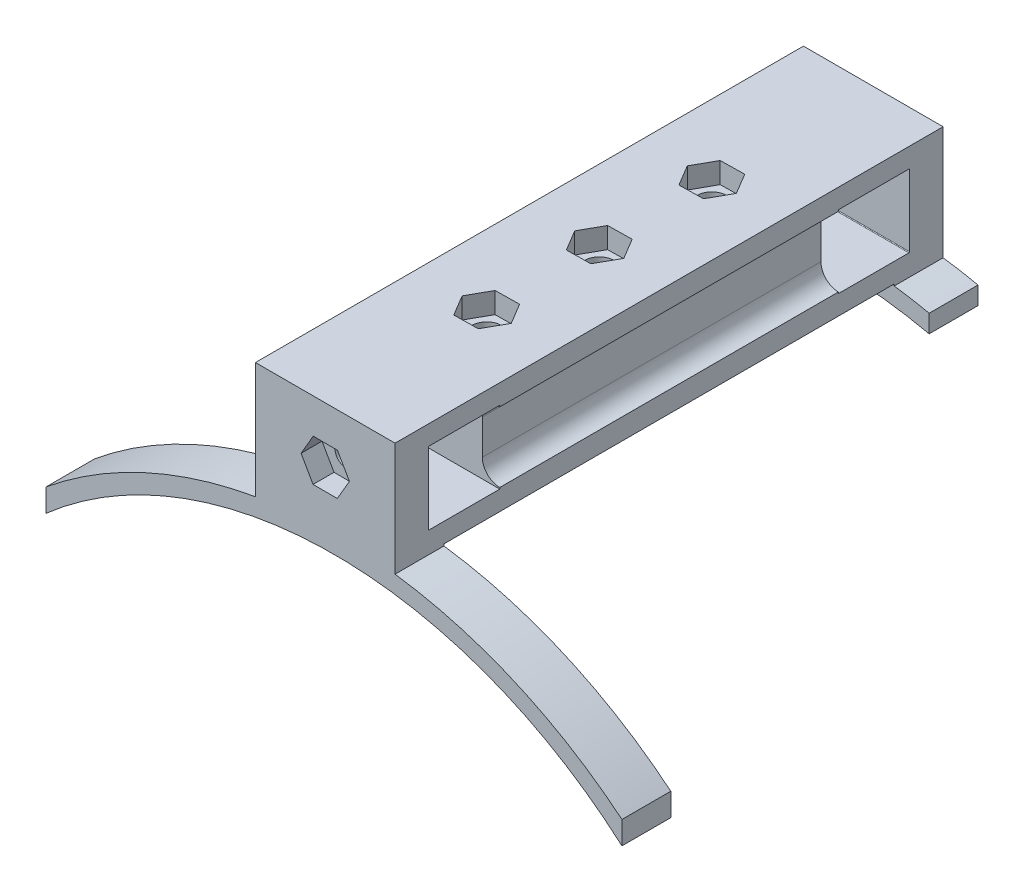
SolidWorks part; units mm, degrees
ref_plane "Front Plane" through (0, 0, 0) normal (0, 0, 1) x (1, 0, 0)
ref_plane "Top Plane" through (0, 0, 0) normal (0, 1, 0) x (1, 0, 0)
ref_plane "Right Plane" through (0, 0, 0) normal (1, 0, 0) x (0, 0, -1)
sketch "Sketch1" plane through (0, 0, 0) normal (0, 0, 1) x (1, 0, 0)
  line L0 (-2.0278, -2.1111) -> (-2.0278, 2.8889)
  line L2 (0.4722, 8.3889) -> (0.4722, 5.3889)
  line L3 (0.4722, -7.6111) -> (0.4722, -4.6111)
  line L9 (0.4722, 8.3889) -> (-17.5278, 8.3889)
  line L10 (0.4722, 8.3889) -> (0.4722, 5.3889)
  line L12 (0.4722, -7.6111) -> (-17.5278, -7.6111)
  line L13 (-17.5278, 8.3889) -> (-17.5278, -7.6111)
  line L14 (0.4722, 8.3889) -> (-17.5278, -7.6111) construction
  line L15 (0.4722, -7.6111) -> (-17.5278, 8.3889) construction
  line L17 (0.4722, -4.6111) -> (0.4722, -7.6111)
  arc A0 (0.4722, 5.3889) -> (-2.0278, 2.8889) centre (0.4722, 2.8889) ccw
  arc A1 (-2.0278, -2.1111) -> (0.4722, -4.6111) centre (0.4722, -2.1111) ccw
  point P14 (-8.5278, 0.3889)
  dimension "D2" = 18
extrude "Boss-Extrude2" add sketch "Sketch1" along normal blind 48.5 contours A1 L0 A0 L2 L9 L13 L12 L3
sketch "Sketch2" plane through (-17.5278, 0, 0) normal (-1, 0, 0) x (0, 0, 1)
  line L0 (48.5, 8.3889) -> (62.5, 8.3889)
  line L1 (63.5, 7.3889) -> (63.5, -6.6111)
  line L2 (62.5, -7.6111) -> (48.5, -7.6111)
  line L3 (58.5, -4.6111) -> (58.5, 5.3889) construction
  line L4 (62.5, 8.3889) -> (63.5, 8.3889)
  line L5 (63.5, 8.3889) -> (63.5, 7.3889)
  line L6 (48.5, 5.3889) -> (58.5, 5.3889) construction
  line L7 (58.5, -4.6111) -> (48.5, -4.6111) construction
  line L8 (48.5, 8.3889) -> (48.5, -7.6111) construction
  line L9 (48.5, 5.5889) -> (58.6, 5.5889)
  line L10 (58.7, -4.7111) -> (58.7, 5.4889)
  line L11 (58.6, -4.8111) -> (48.5, -4.8111)
  line L12 (48.5, 8.3889) -> (48.5, 5.5889)
  line L13 (48.5, -4.8111) -> (48.5, -7.6111)
  line L14 (24.25, 8.3889) -> (24.25, 19.6589) construction
  line L15 (48.5, 8.3889) -> (0, 8.3889) construction
  line L16 (0, -4.8111) -> (0, -7.6111)
  line L17 (0, 8.3889) -> (0, 5.5889)
  line L18 (-10.1, -4.8111) -> (0, -4.8111)
  line L19 (-10.2, -4.7111) -> (-10.2, 5.4889)
  line L20 (0, 5.5889) -> (-10.1, 5.5889)
  line L21 (-14, -7.6111) -> (0, -7.6111)
  line L22 (-15, 7.3889) -> (-15, -6.6111)
  line L23 (0, 8.3889) -> (-14, 8.3889)
  line L24 (63.5, -6.6111) -> (63.5, -7.6111)
  line L25 (63.5, -7.6111) -> (62.5, -7.6111)
  line L26 (-15, 7.3889) -> (-15, 8.3889)
  line L27 (-15, 8.3889) -> (-14, 8.3889)
  line L28 (-15, -6.6111) -> (-15, -7.6111)
  line L29 (-15, -7.6111) -> (-14, -7.6111)
  arc A0 (58.7, -4.7111) -> (58.6, -4.8111) centre (58.6, -4.7111) cw
  arc A1 (58.6, 5.5889) -> (58.7, 5.4889) centre (58.6, 5.4889) cw
  arc A6 (-10.1, 5.5889) -> (-10.2, 5.4889) centre (-10.1, 5.4889) ccw
  arc A7 (-10.2, -4.7111) -> (-10.1, -4.8111) centre (-10.1, -4.7111) ccw
  dimension "D5" = 0.1
  dimension "D1" = 5
  dimension "D2" = 0.2
  dimension "D3" = 0.2
  dimension "D4" = 0.2
extrude "Boss-Extrude3" add sketch "Sketch2" against normal blind 18
sketch "Sketch3" plane through (0, 0, 63.5) normal (0, 0, 1) x (1, 0, 0)
  circle A0 centre (-9.5278, 0.3889) radius 1.6
  dimension "D1" = 3.2
extrude "Cut-Extrude1" cut sketch "Sketch3" against normal blind 8
ref_plane "Plane1" through (0, 0, 24.25) normal (0, 0, 1) x (1, 0, 0)
mirror "Mirror1" about plane through (0, 0, 24.25) normal (0, 0, 1) of "Cut-Extrude1"
sketch "Sketch4" plane through (0, 0, 63.5) normal (0, 0, 1) x (1, 0, 0)
  line L1 (-7.808, -2.6181) -> (-6.0638, 0.3749)
  line L2 (-6.0638, 0.3749) -> (-7.7837, 3.3819)
  line L3 (-7.7837, 3.3819) -> (-11.2477, 3.3959)
  line L4 (-11.2477, 3.3959) -> (-12.9919, 0.4029)
  line L5 (-12.9919, 0.4029) -> (-11.272, -2.604)
  line L6 (-11.272, -2.604) -> (-7.808, -2.6181)
  circle A0 centre (-9.5278, 0.3889) radius 3 construction
  dimension "D1" = 6
extrude "Cut-Extrude3" cut sketch "Sketch4" against normal blind 3
mirror "Mirror2" about plane through (0, 0, 24.25) normal (0, 0, 1) of "Cut-Extrude3"
sketch "Sketch5" plane through (-17.5278, 0, 0) normal (-1, 0, 0) x (0, 0, 1)
  line L4 (-15, -7.6111) -> (63.5, -7.6111)
  line L5 (63.5, -7.6111) -> (63.5, 8.3889)
  line L6 (63.5, 8.3889) -> (-15, 8.3889)
  line L7 (-15, 8.3889) -> (-15, -7.6111)
  line L8 (-15, -7.6111) -> (63.5, -7.6111)
  line L10 (63.5, 8.3889) -> (-15, 8.3889)
  line L11 (-15, 8.3889) -> (-15, -7.6111)
  line L13 (63.5, -7.6111) -> (63.5, 8.3889)
  dimension "D1" = 0
extrude "Boss-Extrude4" add sketch "Sketch5" along normal blind 2
sketch "Sketch6" plane through (0, 0, 63.5) normal (0, 0, 1) x (1, 0, 0)
  line L2 (-19.5278, -7.6111) -> (-19.5278, -8.2571)
  line L3 (-19.5278, -7.6111) -> (0.4722, -7.6111)
  line L4 (0.4722, -7.6111) -> (0.4722, -7.8678)
  line L5 (-39.5278, -15.2811) -> (-39.5278, -18.1496)
  line L6 (-19.5278, -7.6111) -> (-19.5278, 8.3889) construction
  line L7 (22.9722, -15.2811) -> (22.9722, -18.1496)
  line L8 (-19.5278, -7.6111) -> (-19.5278, 8.3889) construction
  line L9 (0.4722, -7.6111) -> (0.4722, 8.3889) construction
  line L10 (0.4722, -7.6111) -> (-19.5278, -7.6111) construction
  arc A0 (-19.5278, -8.2571) -> (-39.5278, -15.2811) centre (-8.2778, -72.2761) ccw
  arc A1 (22.9722, -18.1496) -> (-39.5278, -18.1496) centre (-8.2778, -72.2761) ccw
  arc A2 (22.9722, -15.2811) -> (0.4722, -7.8678) centre (-8.2778, -72.2761) ccw
  point P22 (-9.5278, -7.6111)
  dimension "D2" = 125
  dimension "D4" = 65
  dimension "D3" = 20
extrude "Boss-Extrude5" add sketch "Sketch6" against normal blind 7
mirror "Mirror3" about plane through (0, 0, 24.25) normal (0, 0, 1) of "Boss-Extrude5"
sketch "Sketch7" plane through (0, 0, 63.5) normal (0, 0, 1) x (1, 0, 0)
  line L0 (22.9722, -18.1496) -> (22.9722, -15.2811) construction
  line L1 (-39.5278, -15.2811) -> (-39.5278, -18.1496) construction
  line L2 (22.9722, -18.1496) -> (22.9722, -15.2811)
  line L3 (-39.5278, -15.2811) -> (-39.5278, -18.1496)
  line L4 (-49.5278, -22.0423) -> (-49.5278, -25.322)
  line L5 (-8.2778, -9.7761) -> (-8.2778, -19.2561) construction
  line L6 (32.9722, -22.0423) -> (32.9722, -25.322)
  arc A0 (32.9722, -25.322) -> (22.9722, -18.1496) centre (-8.2778, -72.2761) ccw
  arc A1 (32.9722, -22.0423) -> (22.9722, -15.2811) centre (-8.2778, -72.2761) ccw
  arc A2 (-19.5278, -8.2571) -> (-39.5278, -15.2811) centre (-8.2778, -72.2761) ccw construction
  arc A3 (22.9722, -18.1496) -> (-39.5278, -18.1496) centre (-8.2778, -72.2761) ccw construction
  arc A4 (-39.5278, -18.1496) -> (-49.5278, -25.322) centre (-8.2778, -72.2761) ccw
  arc A5 (-39.5278, -15.2811) -> (-49.5278, -22.0423) centre (-8.2778, -72.2761) ccw
  dimension "D1" = 10
extrude "Boss-Extrude6" add sketch "Sketch7" against normal blind 7
mirror "Mirror4" about plane through (0, 0, 24.25) normal (0, 0, 1) of "Boss-Extrude6"
sketch "Sketch10" plane through (0, -7.6111, 0) normal (0, -1, 0) x (1, 0, 0)
  line L0 (-9.5278, 56.5) -> (-9.5278, 24.25) construction
  line L1 (0.4722, 56.5) -> (-19.5278, 56.5) construction
  line L2 (-9.5278, 24.25) -> (-9.5278, -8) construction
  line L3 (32.9722, -8) -> (-49.5278, -8) construction
  circle A0 centre (-9.5278, 40.375) radius 2.1
  circle A1 centre (-9.5278, 8.125) radius 2.1
  circle A2 centre (-9.5278, 24.25) radius 2.1
  dimension "D1" = 4.2
  dimension "D2" = 4.2
extrude "Cut-Extrude4" cut sketch "Sketch10" against normal through all
sketch "Sketch11" plane through (0, 8.3889, 0) normal (0, 1, 0) x (1, 0, 0)
  line L0 (-7.751, -27.2237) -> (-6.0641, -24.1981)
  line L1 (-7.751, -11.0987) -> (-6.0641, -8.0731)
  line L2 (-6.0641, -8.0731) -> (-7.841, -5.0994)
  line L3 (-7.841, -5.0994) -> (-11.3047, -5.1513)
  line L4 (-11.3047, -5.1513) -> (-12.9916, -8.1769)
  line L5 (-12.9916, -8.1769) -> (-11.2147, -11.1506)
  line L6 (-11.2147, -11.1506) -> (-7.751, -11.0987)
  line L7 (-6.0641, -24.1981) -> (-7.841, -21.2244)
  line L8 (-7.841, -21.2244) -> (-11.3047, -21.2763)
  line L9 (-11.3047, -21.2763) -> (-12.9916, -24.3019)
  line L10 (-12.9916, -24.3019) -> (-11.2147, -27.2756)
  line L11 (-11.2147, -27.2756) -> (-7.751, -27.2237)
  line L12 (-7.751, -43.3487) -> (-6.0641, -40.3231)
  line L13 (-6.0641, -40.3231) -> (-7.841, -37.3494)
  line L14 (-7.841, -37.3494) -> (-11.3047, -37.4013)
  line L15 (-11.3047, -37.4013) -> (-12.9916, -40.4269)
  line L16 (-12.9916, -40.4269) -> (-11.2147, -43.4006)
  line L17 (-11.2147, -43.4006) -> (-7.751, -43.3487)
  circle A0 centre (-9.5278, -8.125) radius 3 construction
  circle A1 centre (-9.5278, -24.25) radius 3 construction
  circle A2 centre (-9.5278, -40.375) radius 3 construction
  dimension "D1" = 6
  dimension "D2" = 3
extrude "Cut-Extrude5" cut sketch "Sketch11" against normal blind 3
sketch "Sketch12" plane through (0, 0, -8) normal (0, 0, 1) x (1, 0, 0)
  line L0 (5.4722, -8.7471) -> (5.4722, -11.3074)
  line L1 (0.4722, -7.8678) -> (0.4722, 8.3889) construction
  line L7 (0.4722, 8.3889) -> (-19.5278, 8.3889)
  line L8 (-19.5278, 8.3889) -> (-19.5278, -8.2571)
  line L9 (-49.5278, -22.0423) -> (-49.5278, -25.322)
  line L10 (32.9722, -25.322) -> (32.9722, -22.0423)
  line L11 (0.4722, -7.8678) -> (0.4722, 8.3889)
  line L15 (32.9722, -25.322) -> (32.9722, -22.0423)
  arc A0 (32.9722, -22.0423) -> (0.4722, -7.8678) centre (-8.2778, -72.2761) ccw construction
  arc A1 (32.9722, -25.322) -> (-49.5278, -25.322) centre (-8.2778, -72.2761) ccw construction
  arc A5 (-19.5278, -8.2571) -> (-49.5278, -22.0423) centre (-8.2778, -72.2761) ccw
  arc A6 (32.9722, -25.322) -> (-49.5278, -25.322) centre (-8.2778, -72.2761) ccw
  arc A7 (32.9722, -22.0423) -> (0.4722, -7.8678) centre (-8.2778, -72.2761) ccw
  arc A9 (32.9722, -25.322) -> (5.4722, -11.3074) centre (-8.2778, -72.2761) ccw
  arc A10 (32.9722, -22.0423) -> (5.4722, -8.7471) centre (-8.2778, -72.2761) ccw
  dimension "D1" = 5
  dimension "D2" = 0
extrude "Cut-Extrude6" cut sketch "Sketch12" against normal through all
